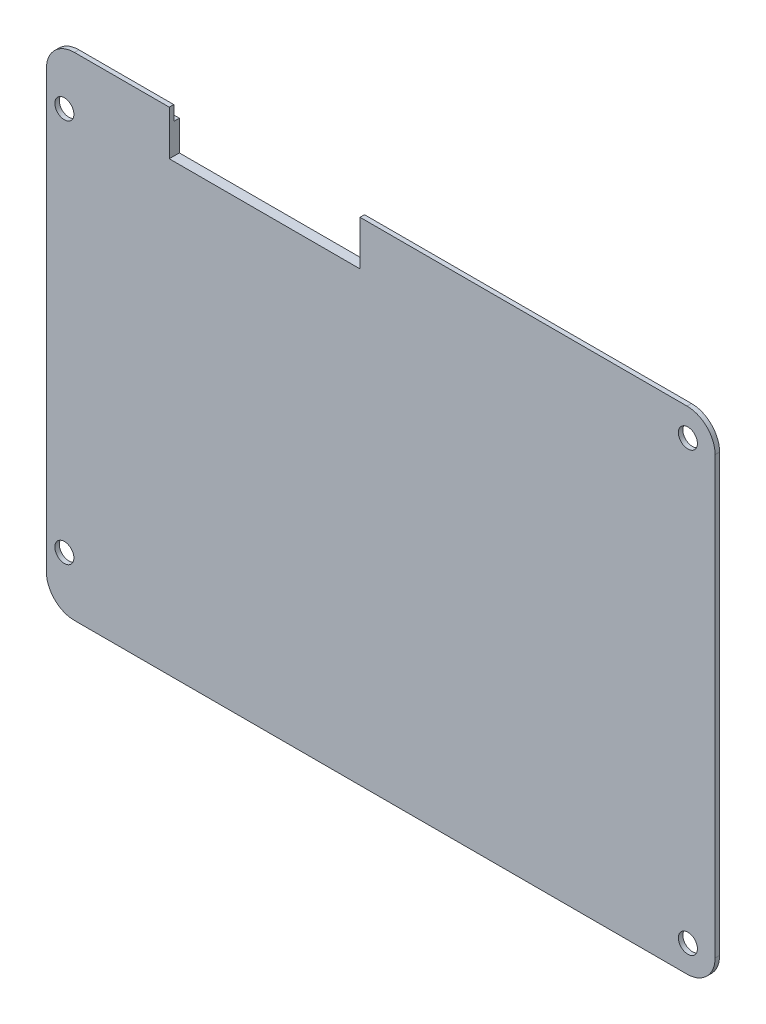
SolidWorks part; units mm, degrees
ref_plane "Front" through (0, 0, 0) normal (0, 0, 1) x (1, 0, 0)
ref_plane "Top" through (0, 0, 0) normal (0, 1, 0) x (1, 0, 0)
ref_plane "Right" through (0, 0, 0) normal (1, 0, 0) x (0, 0, -1)
sketch "Skizze1" plane through (0, 0, 0) normal (0, 0, 1) x (1, 0, 0)
  line L0 (0, 5) -> (0, 82.7)
  line L1 (5, 87.7) -> (21.9, 87.7)
  line L2 (119.2, 82.7) -> (119.2, 75.8)
  line L3 (119.2, 75.8) -> (119.2, 5)
  line L4 (114.2, 0) -> (5, 0)
  line L5 (21.9, 87.7) -> (21.9, 79.7339)
  line L6 (21.9, 79.7339) -> (55.9, 79.7339)
  line L7 (55.9, 79.7339) -> (55.9, 87.7)
  line L8 (55.9, 87.7) -> (114.2, 87.7)
  arc A0 (0, 82.7) -> (5, 87.7) centre (5, 82.7) cw
  arc A1 (114.2, 87.7) -> (119.2, 82.7) centre (114.2, 82.7) cw
  arc A2 (119.2, 5) -> (114.2, 0) centre (114.2, 5) cw
  arc A3 (5, 0) -> (0, 5) centre (5, 5) cw
  circle A4 centre (3.2, 9.6) radius 1.7
  circle A5 centre (3.2, 78.1) radius 1.7
  circle A6 centre (114.35, 82.85) radius 1.7
  circle A7 centre (114.35, 4.85) radius 1.7
  dimension "D1" = 3.4
extrude "Aufsatz-Linear austragen1" add sketch "Skizze1" along normal blind 0.8
sketch "Skizze3" plane through (0, 0, 0) normal (0, 0, -1) x (-1, 0, 0)
  line L0 (-55.9, 85.1) -> (-56.9, 85.1)
  line L1 (-55.9, 87.7) -> (-55.9, 79.7339) construction
  line L2 (-57.1, 83.9) -> (-57.1, 78.5339)
  line L3 (-57.1, 78.5339) -> (-20.7, 78.5339)
  line L4 (-20.7, 78.5339) -> (-20.7, 83.9)
  line L5 (-20.9, 85.1) -> (-21.9, 85.1)
  line L6 (-21.9, 79.7339) -> (-21.9, 87.7) construction
  line L7 (-21.9, 85.1) -> (-21.9, 79.7339)
  line L8 (-21.9, 79.7339) -> (-55.9, 79.7339)
  line L9 (-55.9, 79.7339) -> (-55.9, 85.1)
  line L10 (-117.6, 85.2) -> (-4.6, 85.2) construction
  line L11 (-56.9, 85.1) -> (-105.4586, 85.1)
  line L12 (-105.4586, 85.1) -> (-117.5, 73.0586)
  line L13 (-117.5, 73.0586) -> (-117.5, 14.6414)
  line L14 (-117.5, 14.6414) -> (-105.4586, 2.6)
  line L15 (-105.4586, 2.6) -> (-6.5, 2.6)
  line L16 (-6.5, 2.6) -> (-6.5, 17.2863)
  line L17 (-6.5, 17.2863) -> (-1.7, 22.0863)
  line L18 (-1.7, 22.0863) -> (-1.7, 66.0586)
  line L19 (-1.7, 66.0586) -> (-6.5, 70.8586)
  line L20 (-6.5, 70.8586) -> (-6.5, 85.1)
  line L21 (-6.5, 85.1) -> (-20.9, 85.1)
  line L22 (-6.4, 72.1426) -> (-6.4, 86.1) construction
  line L23 (-2.4787, 66.9787) -> (-5.5213, 70.0213) construction
  line L24 (-1.6, 64.8574) -> (-1.6, 22.8426) construction
  line L25 (-109.4069, 8.4728) -> (-109.5387, 8.3772)
  line L26 (-6.4, 1.6) -> (-6.4, 15.5574) construction
  line L27 (-4.6, 2.5) -> (-117.6, 2.5) construction
  line L28 (-110.6, 7.6) -> (-104.6, 1.6) construction
  line L29 (-117.6, 2.5) -> (-117.6, 85.2) construction
  line L30 (-111.6, 79.1) -> (-113.5936, 77.1064) construction
  line L31 (-57.1, 83.9) -> (-104.9615, 83.9)
  line L32 (-104.9615, 83.9) -> (-116.3, 72.5615)
  line L33 (-116.3, 72.5615) -> (-116.3, 15.1385)
  line L34 (-116.3, 15.1385) -> (-104.9615, 3.8)
  line L35 (-104.9615, 3.8) -> (-7.5, 3.8)
  line L36 (-7.5, 3.8) -> (-7.5, 17.9834)
  line L37 (-7.5, 17.9834) -> (-2.9, 22.5834)
  line L38 (-2.9, 22.5834) -> (-2.9, 65.5615)
  line L39 (-2.9, 65.5615) -> (-7.7, 70.3615)
  line L40 (-7.7, 70.3615) -> (-7.7, 83.9)
  line L41 (-7.7, 83.9) -> (-20.7, 83.9)
  line L42 (-3.1151, 3.1151) -> (-117.7355, 86.2355) construction
  line L43 (-117.7355, 1.4645) -> (-1.4645, 86.2355) construction
  line L44 (-59.444, 4.0274) -> (-59.444, 83.9) construction
  line L45 (-2.5881, 43.9637) -> (-116.3, 43.9637) construction
  line L46 (-108.5477, 80.3138) -> (-60.044, 45.14)
  line L47 (-60.044, 45.14) -> (-60.044, 83.9)
  line L48 (-109.4069, 79.4546) -> (-61.2935, 44.5637)
  line L49 (-61.2935, 44.5637) -> (-116.3, 44.5637)
  line L50 (-60.044, 42.7874) -> (-60.044, 4.0274)
  line L51 (-108.5477, 7.6136) -> (-60.044, 42.7874)
  line L52 (-109.4069, 8.4728) -> (-61.2935, 43.3637)
  line L53 (-61.2935, 43.3637) -> (-116.3, 43.3637)
  line L54 (-7.7, 82.4319) -> (-58.844, 45.1437)
  line L55 (-58.844, 45.1437) -> (-58.844, 83.9)
  line L56 (-7.7, 80.9468) -> (-57.6026, 44.5637)
  line L57 (-57.6026, 44.5637) -> (-2.9, 44.5637)
  line L58 (-57.6026, 43.3637) -> (-2.9, 43.3637)
  line L59 (-7.7, 6.9806) -> (-57.6026, 43.3637)
  line L60 (-7.7, 5.4956) -> (-58.844, 42.7837)
  line L61 (-58.844, 42.7837) -> (-58.844, 4.0274)
  line L62 (-108.5477, 7.6136) -> (-108.6795, 7.518)
  line L63 (-58.844, 4.0274) -> (-58.844, 3.8)
  line L64 (-60.044, 4.0274) -> (-60.044, 3.8)
  line L65 (-7.7, 6.9806) -> (-7.5, 6.8348)
  line L66 (-7.7, 5.4956) -> (-7.5, 5.3497)
  arc A0 (-4.6, 2.5) -> (-2.5, 4.6) centre (-4.6, 4.6) ccw construction
  arc A1 (-114.2, 87.7) -> (-119.2, 82.7) centre (-114.2, 82.7) ccw construction
  arc A2 (-119.2, 5) -> (-114.2, 0) centre (-114.2, 5) ccw construction
  arc A3 (0, 82.7) -> (-5, 87.7) centre (-5, 82.7) ccw construction
  point P74 (-59.444, 43.9637)
  line M49 (-21.9, 87.7) -> (-21.9, 79.7339)
  line M50 (-21.9, 79.7339) -> (-55.9, 79.7339)
  line M51 (-55.9, 79.7339) -> (-55.9, 87.7)
  dimension "D1" = 0.1
  dimension "D2" = 1.2
  dimension "D3" = 1.2
  dimension "D4" = 1.2
  dimension "D5" = 0.1
  dimension "D6" = 0.1
  dimension "D7" = 0.1
  dimension "D8" = 0.1
  dimension "D9" = 0.1
  dimension "D10" = 0.1
  dimension "D11" = 0.1
  dimension "D12" = 0.1
  dimension "D13" = 1.2
  dimension "D14" = 1.2
  dimension "D15" = 1.2
  dimension "D16" = 1.2
  dimension "D17" = 1.2
  dimension "D18" = 1
  dimension "D19" = 1.2
  dimension "D20" = 1.2
  dimension "D21" = 1.2
  dimension "D22" = 1.2
  dimension "D23" = 1.2
  dimension "D24" = 1.2
  dimension "D25" = 0.6
  dimension "D26" = 0.6
  dimension "D27" = 0.6
  dimension "D28" = 0.6
  dimension "D29" = 0.6
  dimension "D30" = 0.6
extrude "Aufsatz-Linear austragen2" add sketch "Skizze3" along normal blind 1 contours L20 L21 L5 L0 L11 L12 L13 L14 L15 L16 L17 L18 L19 L41 L40 L39 L38 L37 L36 L35 L34 L33 L32 L31 L2 L3 L4 M49 M50 M51 | L50 L64 L35 L63 L61 L60 L36 L59 L58 L38 L57 L56 L40 L54 L55 L31 L47 L46 L32 L48 L49 L33 L53 L52 L25 L34 L62 L51
